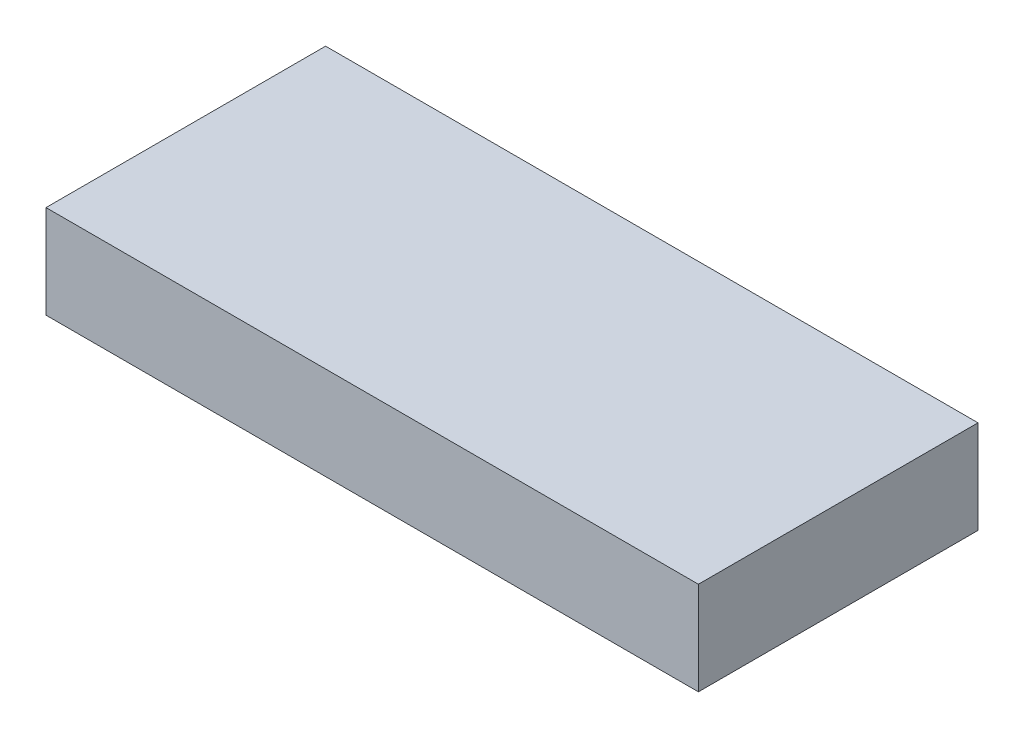
SolidWorks part; units mm, degrees
ref_plane "Front Plane" through (0, 0, 0) normal (0, 0, 1) x (1, 0, 0)
ref_plane "Top Plane" through (0, 0, 0) normal (0, 1, 0) x (1, 0, 0)
ref_plane "Right Plane" through (0, 0, 0) normal (1, 0, 0) x (0, 0, -1)
sketch "Sketch1" plane through (0, 0, 0) normal (0, 1, 0) x (1, 0, 0)
  line L0 (-8.89, -3.81) -> (8.89, 3.81) construction
  line L1 (-8.89, 3.81) -> (8.89, 3.81)
  line L2 (-8.89, 3.81) -> (-8.89, -3.81)
  line L3 (-8.89, -3.81) -> (8.89, -3.81)
  line L4 (8.89, 3.81) -> (8.89, -3.81)
  point P4 (0, 0)
  dimension "D1" = 17.78
  dimension "D2" = 7.62
extrude "Extrude1" add sketch "Sketch1" along normal blind 2.54
